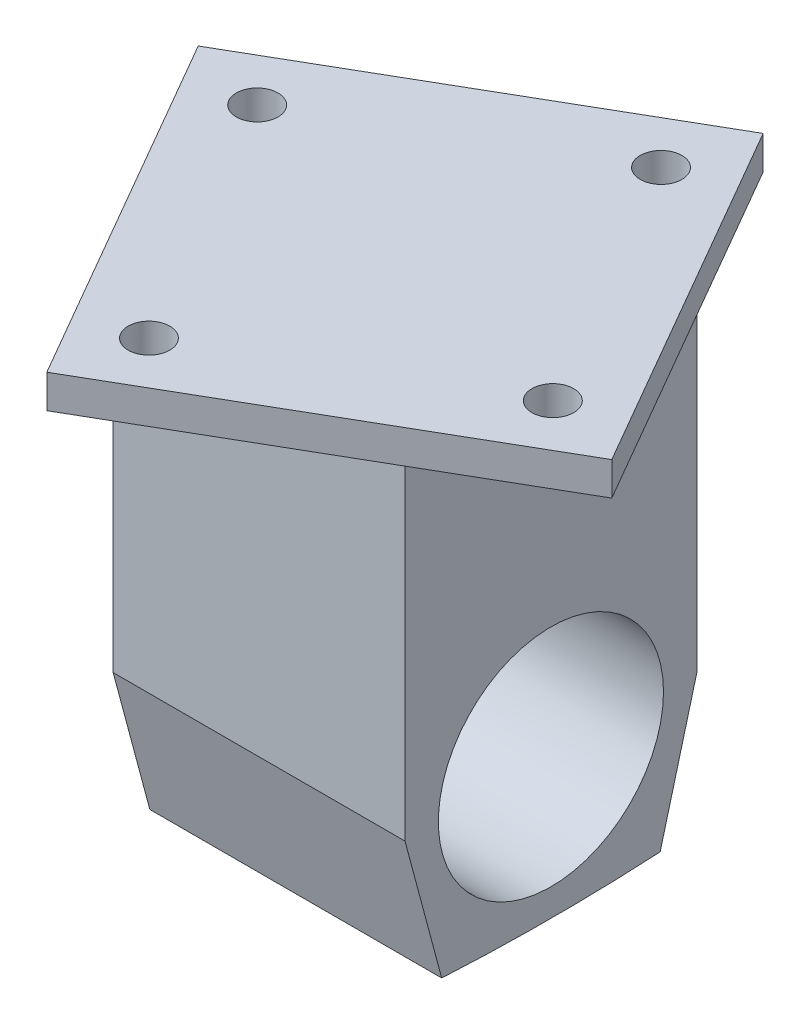
SolidWorks part; units mm, degrees
material "ABS"
ref_plane "Front Plane" through (0, 0, 0) normal (0, 0, 1) x (1, 0, 0)
ref_plane "Top Plane" through (0, 0, 0) normal (0, 1, 0) x (1, 0, 0)
ref_plane "Right Plane" through (0, 0, 0) normal (1, 0, 0) x (0, 0, -1)
sketch "Sketch1" plane through (0, 0, 0) normal (0, 1, 0) x (1, 0, 0)
  line L1 (-22.225, -22.225) -> (22.225, -22.225)
  line L2 (-22.225, -22.225) -> (-22.225, 22.225)
  line L3 (-22.225, 22.225) -> (22.225, 22.225)
  line L4 (22.225, -22.225) -> (22.225, 22.225)
  line L5 (-22.225, -22.225) -> (22.225, 22.225) construction
  line L6 (-22.225, 22.225) -> (22.225, -22.225) construction
  point P0 (0, 0)
extrude "Boss-Extrude1" add sketch "Sketch1" along normal blind 50.292
sketch "Sketch2" plane through (22.225, 0, 0) normal (1, 0, 0) x (0, 0, -1)
  line L0 (-22.225, 0) -> (-16.6371, -20.8543)
  line L1 (22.225, 0) -> (16.6371, -20.8543)
  line L2 (-22.225, 0) -> (22.225, 0)
  line L3 (-22.225, 0) -> (22.225, 0) construction
  arc A1 (16.6371, -20.8543) -> (-16.6371, -20.8543) centre (0, 278.6719) cw
  dimension "D1" = 21.59
  dimension "D2" = 21.59
  dimension "D3" = 75
  dimension "D4" = 75
extrude "Boss-Extrude2" add sketch "Sketch2" against normal up to vertex (44.45 mm away) contours L0 A1 L1 L2 up to point (-22.225, 0, -22.225)
sketch "Sketch3" plane through (22.225, 0, 0) normal (1, 0, 0) x (0, 0, -1)
  circle A0 centre (0, 0) radius 17.145
extrude "Cut-Extrude1" cut sketch "Sketch3" against normal blind 127 contours A0
sketch "Sketch4" plane through (0, 50.292, 0) normal (0, 1, 0) x (1, 0, 0)
  line L0 (-46.8473, 12.5527) -> (46.8473, -12.5527) construction
  line L5 (-13.6389, -50.901) -> (13.6389, 50.901) construction
  line L6 (43.0243, -11.5283) -> (-11.5283, -43.0243)
  line L11 (-11.5283, -43.0243) -> (-43.0243, 11.5283)
  line L12 (-43.0243, 11.5283) -> (11.5283, 43.0243)
  line L13 (11.5283, 43.0243) -> (43.0243, -11.5283)
  line L14 (-11.5283, -43.0243) -> (11.5283, 43.0243) construction
  line L15 (-43.0243, 11.5283) -> (43.0243, -11.5283) construction
  point P1 (0, 0)
  point P4 (0, 0)
  point P11 (0, 0)
  dimension "D1" = 62.992
  dimension "D2" = 62.992
  dimension "D3" = 0
  dimension "D4" = 0
extrude "Boss-Extrude3" add sketch "Sketch4" along normal blind 5.08
sketch "Sketch5" plane through (0, 55.372, 0) normal (0, 1, 0) x (1, 0, 0)
  line L2 (30.7571, -8.2413) -> (43.0243, -11.5283) construction
  line L3 (-8.2413, -30.7571) -> (-11.5283, -43.0243) construction
  line L4 (-30.7571, 8.2413) -> (-43.0243, 11.5283) construction
  line L5 (8.2413, 30.7571) -> (11.5283, 43.0243) construction
  line L6 (11.5283, 43.0243) -> (-43.0243, 11.5283) construction
  line L7 (43.0243, -11.5283) -> (11.5283, 43.0243) construction
  line L8 (-43.0243, 11.5283) -> (-11.5283, -43.0243) construction
  circle A0 centre (30.7571, -8.2413) radius 3.175
  circle A1 centre (-8.2413, -30.7571) radius 3.175
  circle A2 centre (8.2413, 30.7571) radius 3.175
  circle A3 centre (-30.7571, 8.2413) radius 3.175
  dimension "D2" = 6.35
  dimension "D4" = 6.35
  dimension "D11" = 6.35
  dimension "D12" = 6.35
  dimension "D1" = 12.7
  dimension "D3" = 45
  dimension "D5" = 12.7
  dimension "D6" = 45
  dimension "D7" = 12.7
  dimension "D8" = 45
  dimension "D9" = 12.7
  dimension "D10" = 45
extrude "Cut-Extrude2" cut sketch "Sketch5" against normal through all
